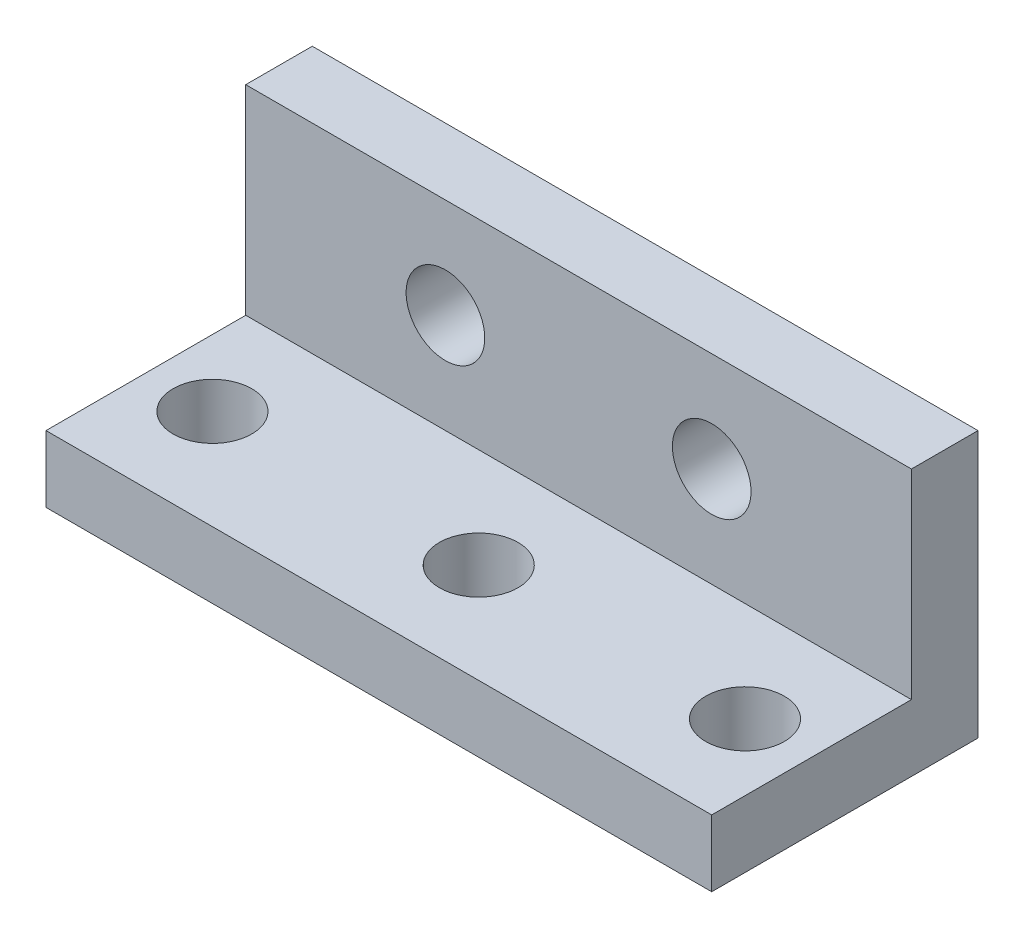
SolidWorks part; units mm, degrees
material "1060 Alloy"
ref_plane "Front Plane" through (0, 0, 0) normal (0, 0, 1) x (1, 0, 0)
ref_plane "Top Plane" through (0, 0, 0) normal (0, 1, 0) x (1, 0, 0)
ref_plane "Right Plane" through (0, 0, 0) normal (1, 0, 0) x (0, 0, -1)
sketch "Sketch1" plane through (0, 0, 0) normal (1, 0, 0) x (0, 0, -1)
  line L1 (0, 0) -> (10.16, 0)
  line L2 (0, 0) -> (0, 10.16)
  line L3 (0, 10.16) -> (10.16, 10.16)
  line L4 (10.16, 0) -> (10.16, 10.16)
  dimension "D1" = 10.16
extrude "Boss-Extrude1" add sketch "Sketch1" along normal blind 25.4
sketch "Sketch2" plane through (25.4, 0, 0) normal (1, 0, 0) x (0, 0, -1)
  line L1 (0, 10.16) -> (7.62, 10.16)
  line L2 (0, 10.16) -> (0, 2.54)
  line L3 (0, 2.54) -> (7.62, 2.54)
  line L4 (7.62, 10.16) -> (7.62, 2.54)
  dimension "D1" = 7.62
extrude "Cut-Extrude1" cut sketch "Sketch2" against normal through all
sketch "Sketch3" plane through (0, 0, -7.62) normal (0, 0, 1) x (1, 0, 0)
  line L0 (7.62, 6.35) -> (17.78, 6.35) construction
  line L1 (12.7, 6.35) -> (12.7, 10.16) construction
  line L2 (0, 10.16) -> (25.4, 10.16) construction
  line L3 (17.78, 6.35) -> (25.4, 6.35) construction
  line L4 (25.4, 2.54) -> (25.4, 10.16) construction
  circle A0 centre (7.62, 6.35) radius 1.5
  circle A1 centre (17.78, 6.35) radius 1.5
  dimension "D2" = 3
  dimension "D1" = 10.16
extrude "Cut-Extrude2" cut sketch "Sketch3" against normal through all
sketch "Sketch4" plane through (0, 2.54, 0) normal (0, 1, 0) x (1, 0, 0)
  line L0 (2.54, 3.81) -> (22.86, 3.81) construction
  line L1 (22.86, 3.81) -> (25.4, 3.81) construction
  line L2 (25.4, 0) -> (25.4, 7.62) construction
  line L3 (12.7, 3.81) -> (12.7, 0) construction
  line L4 (0, 0) -> (25.4, 0) construction
  line L5 (0, 0) -> (0, 7.62) construction
  circle A0 centre (2.54, 3.81) radius 1.5
  circle A1 centre (22.86, 3.81) radius 1.5
  circle A2 centre (12.7, 3.81) radius 1.5
  dimension "D1" = 3
  dimension "D2" = 2.54
extrude "Cut-Extrude3" cut sketch "Sketch4" against normal through all
